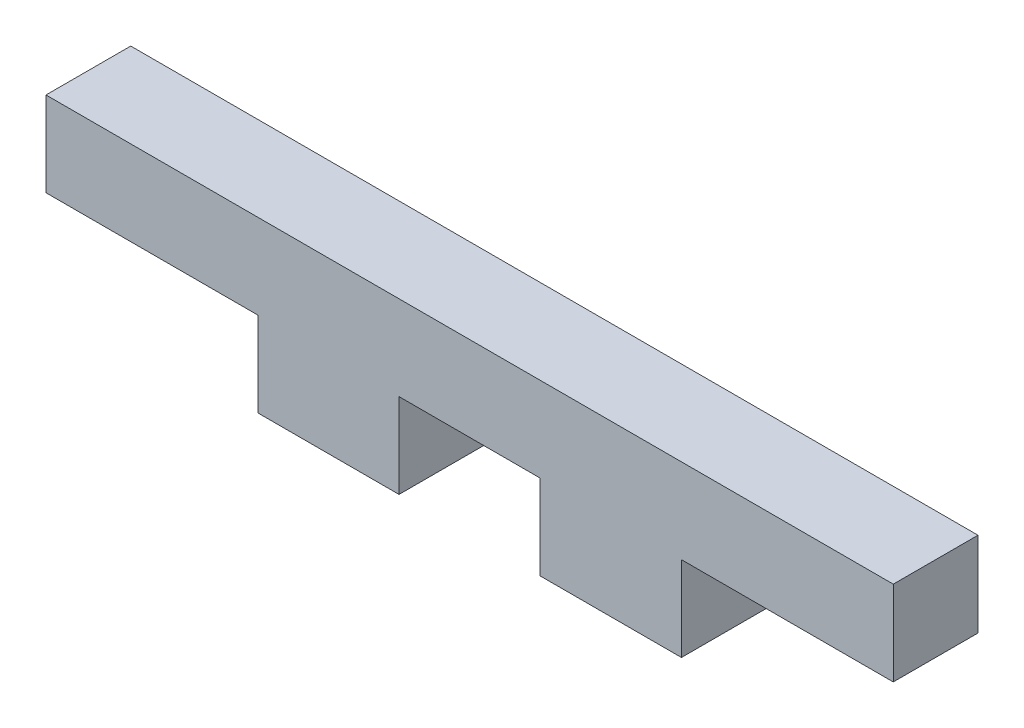
SolidWorks part; units mm, degrees
ref_plane "Plan de face" through (0, 0, 0) normal (0, 0, 1) x (1, 0, 0)
ref_plane "Plan de dessus" through (0, 0, 0) normal (0, 1, 0) x (1, 0, 0)
ref_plane "Plan de droite" through (0, 0, 0) normal (1, 0, 0) x (0, 0, -1)
sketch "Esquisse1" plane through (0, 0, 0) normal (0, 0, 1) x (1, 0, 0)
  line L0 (13.9901, 0.1004) -> (13.9901, -2.8996)
  line L1 (3.9901, 0.1004) -> (8.9901, 0.1004)
  line L2 (3.9901, 0.1004) -> (3.9901, -2.8996)
  line L3 (3.9901, -2.8996) -> (8.9901, -2.8996)
  line L4 (8.9901, 0.1004) -> (8.9901, -2.8996)
  line L5 (26.4901, 3.1004) -> (-3.5099, 3.1004)
  line L6 (26.4901, 3.1004) -> (26.4901, 0.1004)
  line L7 (26.4901, 0.1004) -> (-3.5099, 0.1004)
  line L8 (-3.5099, 3.1004) -> (-3.5099, 0.1004)
  line L9 (13.9901, -2.8996) -> (18.9901, -2.8996)
  line L10 (18.9901, 0.1004) -> (18.9901, -2.8996)
  dimension "D1" = 3
  dimension "D2" = 30
  dimension "D3" = 5
  dimension "D6" = 3
  dimension "D7" = 7.5
extrude "Boss.-Extru.1" add sketch "Esquisse1" along normal blind 3
